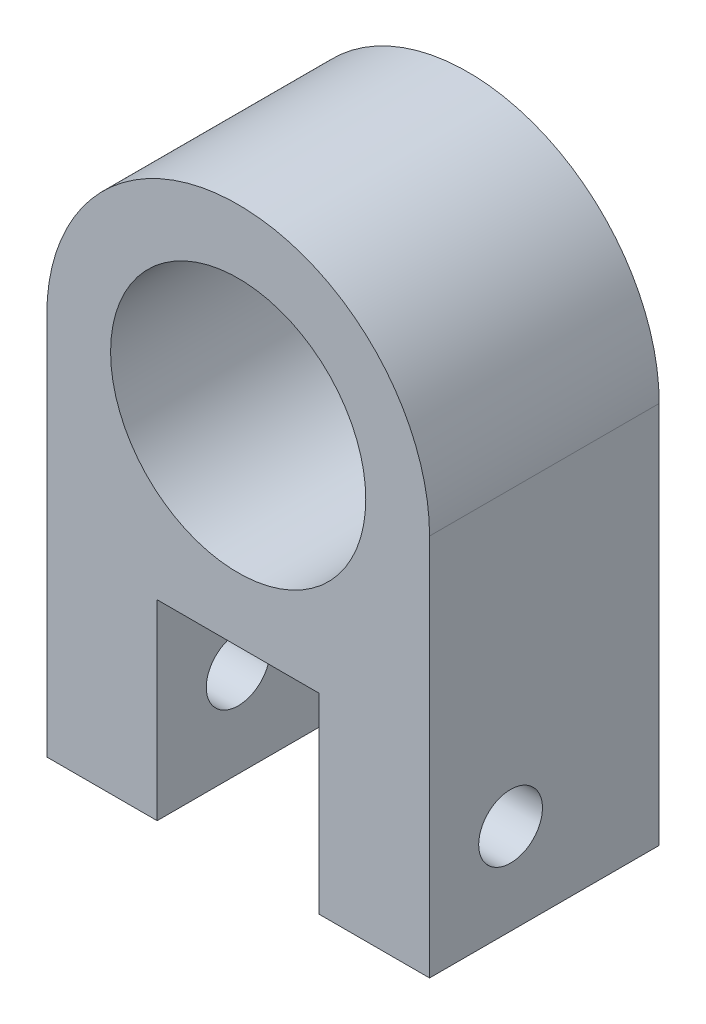
SolidWorks part; units mm, degrees
ref_plane "Plan de face" through (0, 0, 0) normal (0, 0, 1) x (1, 0, 0)
ref_plane "Plan de dessus" through (0, 0, 0) normal (0, 1, 0) x (1, 0, 0)
ref_plane "Plan de droite" through (0, 0, 0) normal (1, 0, 0) x (0, 0, -1)
sketch "Esquisse1" plane through (0, 0, 0) normal (0, 0, 1) x (1, 0, 0)
  line L0 (0, 0) -> (30, 0)
  line L1 (30, 0) -> (30, 30)
  line L2 (0, 0) -> (0, 30)
  line L3 (15, 0) -> (15, 58.6064) construction
  circle A0 centre (15, 30) radius 10
  arc A1 (0, 30) -> (30, 30) centre (15, 30) cw
  point P3 (15, 20)
  dimension "D3" = 20
  dimension "D4" = 5
  dimension "D1" = 30
  dimension "D2" = 20
extrude "Boss.-Extru.1" add sketch "Esquisse1" along normal blind 18
sketch "Esquisse2" plane through (0, 0, 18) normal (0, 0, 1) x (1, 0, 0)
  line L0 (0, 0) -> (30, 0) construction
  line L1 (8.65, 15) -> (21.35, 15)
  line L2 (8.65, 15) -> (8.65, 0)
  line L3 (8.65, 0) -> (21.35, 0)
  line L4 (21.35, 15) -> (21.35, 0)
  line L5 (8.65, 15) -> (21.35, 0) construction
  line L6 (8.65, 0) -> (21.35, 15) construction
  line L9 (15, 25.1696) -> (15, -2.2391) construction
  line L10 (0, 30) -> (0, 0) construction
  line L11 (30, 0) -> (30, 30) construction
  point P0 (15, 7.5)
  dimension "D1" = 15
  dimension "D2" = 12.7
extrude "Enlèv. mat.-Extru.1" cut sketch "Esquisse2" against normal blind 12.7
sketch "Esquisse3" plane through (0, 0, 0) normal (-1, 0, 0) x (0, 0, 1)
  line L0 (5.3, 0) -> (5.3, 15) construction
  line L1 (18, 0) -> (0, 0) construction
  line L2 (5.3, 15) -> (18, 15) construction
  line L3 (18, 30) -> (18, 0) construction
  line L4 (5.3, 15) -> (18, 15) construction
  line L5 (5.3, 15) -> (5.3, 0) construction
  line L6 (11.65, 15) -> (11.65, 0) construction
  circle A0 centre (11.65, 7.125) radius 2.5
  dimension "D1" = 5
  dimension "D2" = 7.125
extrude "Enlèv. mat.-Extru.2" cut sketch "Esquisse3" against normal through all
